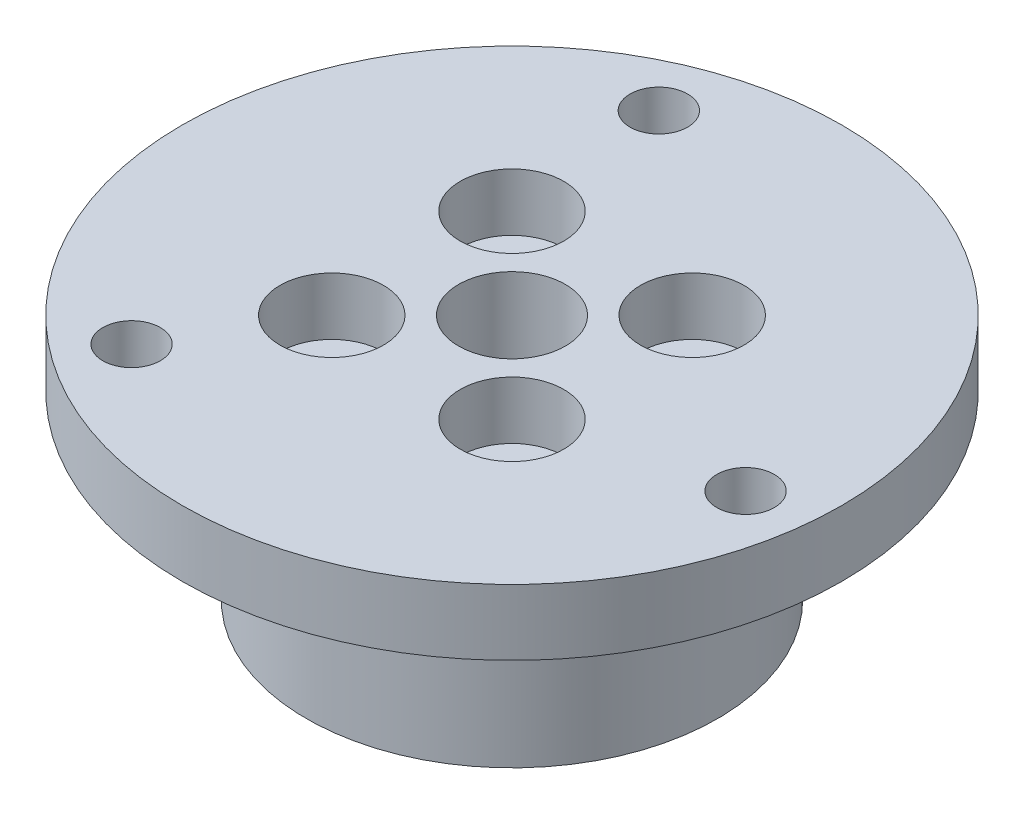
SolidWorks part; units mm, degrees
ref_plane "前基準面" through (0, 0, 0) normal (0, 0, 1) x (1, 0, 0)
ref_plane "上基準面" through (0, 0, 0) normal (0, 1, 0) x (1, 0, 0)
ref_plane "右基準面" through (0, 0, 0) normal (1, 0, 0) x (0, 0, -1)
sketch "Sketch1" plane through (0, 0, 0) normal (0, 1, 0) x (1, 0, 0)
  line L0 (0, 0) -> (-6.3143, 15.244) construction
  line L5 (-5.4801, 5.4801) -> (-5.4801, -5.4801) construction
  line L7 (0, 0) -> (0, 21.4212) construction
  circle A1 centre (0, 0) radius 3.25
  circle A2 centre (5.4801, 5.4801) radius 1.75
  circle A3 centre (5.4801, -5.4801) radius 1.75
  circle A4 centre (-5.4801, -5.4801) radius 1.75
  circle A5 centre (-5.4801, 5.4801) radius 1.75
  circle A6 centre (-10.0446, -13.0903) radius 1.75
  circle A7 centre (-6.3143, 15.244) radius 1.75
  circle A8 centre (16.3588, -2.1537) radius 1.75
  circle A9 centre (0, 0) radius 20.05
  point P15 (0, 0)
  point P25 (0, 0)
  dimension "D2" = 6.5
  dimension "D5" = 3.5
  dimension "D8" = 3.5
  dimension "D11" = 40.1
  dimension "D4" = 15.5
  dimension "D6" = 22.5
  dimension "D10" = 16.5
  dimension "D3" = 4
  dimension "D9" = 3
extrude "Extrude1" add sketch "Sketch1" along normal blind 15
sketch "Sketch7" plane through (0, 15, 0) normal (0, 1, 0) x (1, 0, 0)
  circle A0 centre (-5.4801, 5.4801) radius 3.15
  circle A1 centre (5.4801, 5.4801) radius 3.15
  circle A2 centre (5.4801, -5.4801) radius 3.15
  circle A3 centre (-5.4801, -5.4801) radius 3.15
  dimension "D1" = 6.3
extrude "Extrude4" cut sketch "Sketch7" against normal blind 3.5
sketch "Sketch8" plane through (0, 0, 0) normal (0, -1, 0) x (1, 0, 0)
  circle A0 centre (0, 0) radius 20.05
  circle A1 centre (0, 0) radius 12.5
  dimension "D1" = 25
extrude "Extrude5" cut sketch "Sketch8" against normal blind 11
